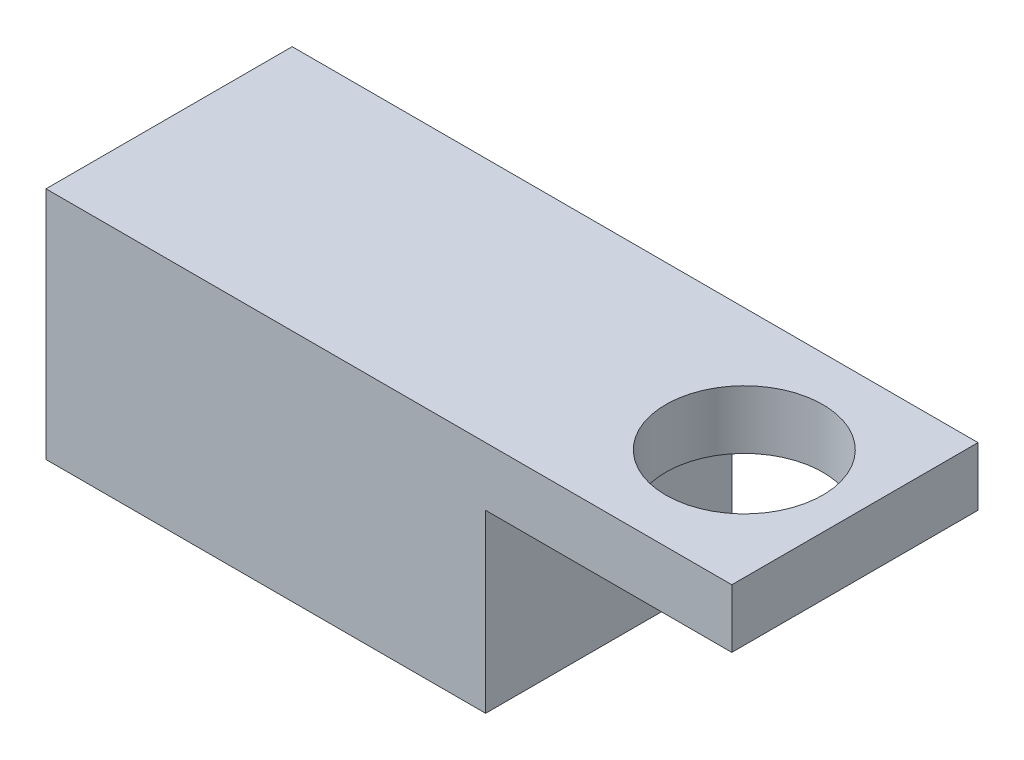
SolidWorks part; units mm, degrees
ref_plane "Front Plane" through (0, 0, 0) normal (0, 0, 1) x (1, 0, 0)
ref_plane "Top Plane" through (0, 0, 0) normal (0, 1, 0) x (1, 0, 0)
ref_plane "Right Plane" through (0, 0, 0) normal (1, 0, 0) x (0, 0, -1)
sketch "Sketch1" plane through (0, 0, 0) normal (0, 1, 0) x (1, 0, 0)
  line L1 (-14.859, -5.334) -> (14.859, -5.334)
  line L2 (-14.859, -5.334) -> (-14.859, 5.334)
  line L3 (-14.859, 5.334) -> (14.859, 5.334)
  line L4 (14.859, -5.334) -> (14.859, 5.334)
  line L5 (-14.859, -5.334) -> (14.859, 5.334) construction
  line L6 (-14.859, 5.334) -> (14.859, -5.334) construction
  point P0 (0, 0)
  dimension "D1" = 10.668
  dimension "D2" = 29.718
extrude "Boss-Extrude1" add sketch "Sketch1" along normal blind 10.16
sketch "Sketch2" plane through (0, 0, 0) normal (0, -1, 0) x (-1, 0, 0)
  line L0 (-14.859, -5.334) -> (-14.859, 5.334) construction
  line L1 (-14.859, -5.334) -> (-4.191, -5.334)
  line L2 (-14.859, -5.334) -> (-14.859, 5.334)
  line L3 (-14.859, 5.334) -> (-4.191, 5.334)
  line L4 (-4.191, -5.334) -> (-4.191, 5.334)
  line L5 (-14.859, 5.334) -> (14.859, 5.334) construction
  line L6 (14.859, 5.334) -> (14.859, -5.334) construction
  line L7 (14.859, -5.334) -> (-14.859, -5.334) construction
  dimension "D1" = 19.05
extrude "Cut-Extrude1" cut sketch "Sketch2" against normal blind 7.62
hole_wizard "M6 Clearance Hole1" positions "Sketch3" profile "Sketch4" hole size "M6" standard "ANSI Metric"
sketch "Sketch3" plane through (0, 10.16, 0) normal (0, 1, 0) x (1, 0, 0)
  line L0 (-14.859, 5.334) -> (-14.859, -5.334) construction
  point P0 (10.066, 0)
  dimension "D1" = 24.925
sketch "Sketch4" plane through (10.066, 10.16, 0) normal (1, 0, 0) x (0, 0, 1)
  line L0 (0, 0) -> (0, 34.5432)
  line L1 (0, 34.5432) -> (3.4016, 32.4993)
  line L2 (3.4016, 32.4993) -> (3.4016, 0)
  line L5 (3.4016, 0) -> (0, 0)
  line L10 (0, 34.5432) -> (-3.4016, 32.4993) construction
  line L11 (0, -6.35) -> (0, 107.95) construction
  dimension "Hole Dia." = 6.8032
  dimension "Hole Depth" = 32.4993
  dimension "Drill Angle" = 118
